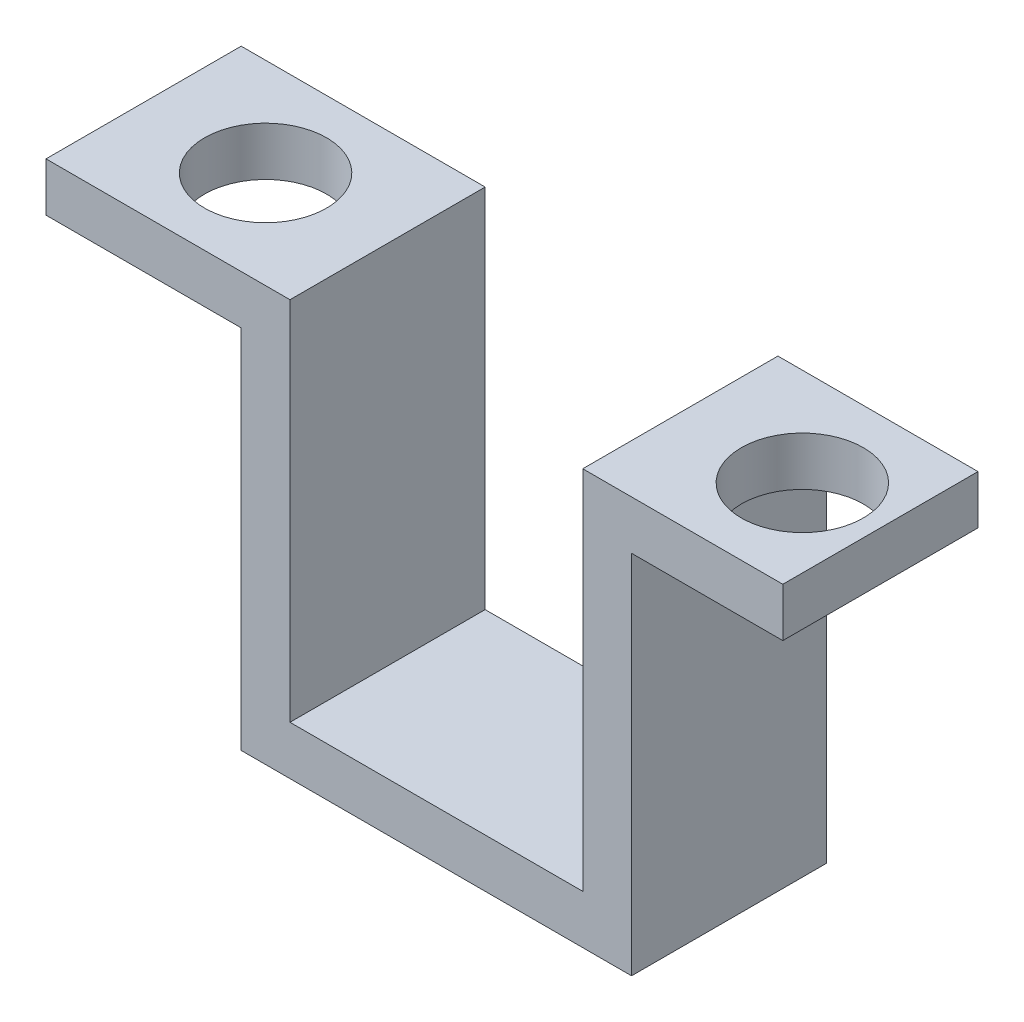
SolidWorks part; units mm, degrees
ref_plane "Alzado" through (0, 0, 0) normal (0, 0, 1) x (1, 0, 0)
ref_plane "Planta" through (0, 0, 0) normal (0, 1, 0) x (1, 0, 0)
ref_plane "Vista lateral" through (0, 0, 0) normal (1, 0, 0) x (0, 0, -1)
sketch "Croquis1" plane through (0, 0, 0) normal (0, 0, 1) x (1, 0, 0)
  line L0 (-6, 7.5) -> (-8, 7.5)
  line L1 (-6, -7.5) -> (6, -7.5)
  line L2 (-6, -7.5) -> (-6, 7.5)
  line L4 (6, -7.5) -> (6, 7.5)
  line L5 (-6, -7.5) -> (6, 7.5) construction
  line L6 (-6, 7.5) -> (6, -7.5) construction
  line L7 (8, 7.5) -> (6, 7.5)
  line L8 (8, 5.5) -> (8, -9.5)
  line L9 (8, -9.5) -> (-8, -9.5)
  line L10 (-8, 5.5) -> (-8, -9.5)
  line L11 (8, 7.5) -> (16, 7.5)
  line L12 (8, 7.5) -> (8, 5.5)
  line L13 (8, 5.5) -> (16, 5.5)
  line L14 (16, 7.5) -> (16, 5.5)
  line L15 (-8, 7.5) -> (-16, 7.5)
  line L16 (-8, 7.5) -> (-8, 5.5)
  line L17 (-8, 5.5) -> (-16, 5.5)
  line L18 (-16, 7.5) -> (-16, 5.5)
  point P0 (0, 0)
  dimension "D1" = 12
  dimension "D2" = 15
  dimension "D3" = 2
  dimension "D4" = 2
  dimension "D5" = 17
  dimension "D6" = 8
  dimension "D7" = 2
  dimension "D8" = 2
  dimension "D9" = 8
extrude "Saliente-Extruir1" add sketch "Croquis1" along normal blind 8 contours L15 L18 L17 L16 | L0 L16 L10 L9 L8 L12 L7 L4 L1 L2 | L14 L11 L12 L13
sketch "Croquis2" plane through (0, 7.5, 0) normal (0, 1, 0) x (1, 0, 0)
  line L0 (-16, -4) -> (-11, -4) construction
  line L1 (-16, -8) -> (-16, 0) construction
  line L2 (-11, 0) -> (-11, -4) construction
  line L3 (-6, 0) -> (-16, 0) construction
  line L4 (16, -4) -> (11, -4) construction
  line L5 (16, -8) -> (16, 0) construction
  line L6 (11, 0) -> (11, -4) construction
  line L7 (16, 0) -> (6, 0) construction
  circle A0 centre (-11, -4) radius 2.5
  circle A1 centre (11, -4) radius 2.5
  dimension "D1" = 5
  dimension "D2" = 5
extrude "Cortar-Extruir1" cut sketch "Croquis2" against normal blind 2
sketch "Sketch1" plane through (16, 0, 0) normal (1, 0, 0) x (0, 0, -1)
  line L1 (-8, 7.5) -> (0, 7.5)
  line L2 (-8, 7.5) -> (-8, 5.5)
  line L3 (-8, 5.5) -> (0, 5.5)
  line L4 (0, 7.5) -> (0, 5.5)
extrude "Cut-Extrude1" cut sketch "Sketch1" against normal blind 1.8
